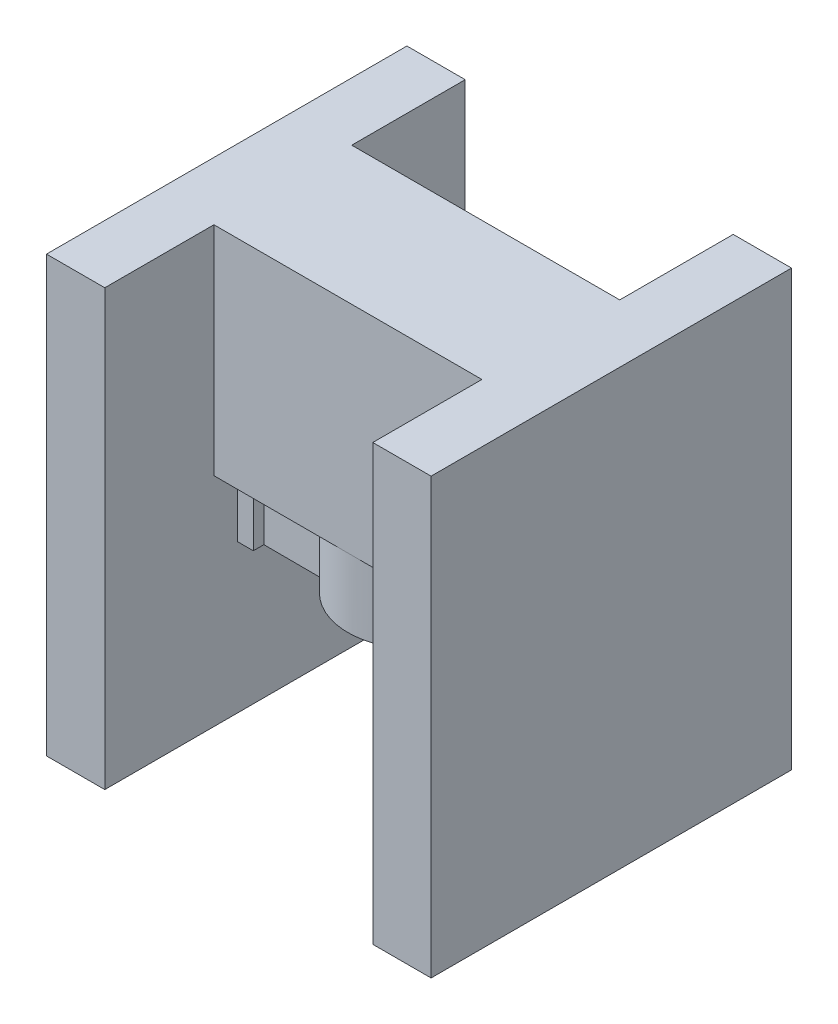
SolidWorks part; units mm, degrees
ref_plane "Front Plane" through (0, 0, 0) normal (0, 0, 1) x (1, 0, 0)
ref_plane "Top Plane" through (0, 0, 0) normal (0, 1, 0) x (1, 0, 0)
ref_plane "Right Plane" through (0, 0, 0) normal (1, 0, 0) x (0, 0, -1)
sketch "Sketch1" plane through (0, 0, 0) normal (0, 1, 0) x (1, 0, 0)
  line L0 (118.5, 375) -> (592.5, 375) construction
  line L1 (24.82, 34.4098) -> (19.2722, 34.4309)
  line L2 (19.2722, 34.4309) -> (19.2722, 33.4309)
  line L3 (17.7797, 42.2353) -> (19.2722, 42.2353)
  line L5 (17.7797, 33.4309) -> (19.2722, 33.4309)
  line L6 (19.2722, 42.2353) -> (19.2722, 40.86)
  line L7 (43.0607, 54.9144) -> (43.0607, 42.2353)
  line L8 (48.5607, 54.9144) -> (43.0607, 54.9144)
  line L9 (48.5607, 20.9144) -> (48.5607, 54.9144)
  line L10 (43.0607, 20.9144) -> (48.5607, 20.9144)
  line L11 (36.0204, 34.4098) -> (41.5682, 34.4309)
  line L13 (41.5682, 40.86) -> (36.1056, 40.86)
  line L14 (17.7797, 33.4309) -> (17.7797, 20.9144)
  line L15 (17.7797, 20.9144) -> (12.2797, 20.9144)
  line L16 (12.2797, 20.9144) -> (12.2797, 54.9144)
  line L17 (12.2797, 54.9144) -> (17.7797, 54.9144)
  line L18 (17.7797, 54.9144) -> (17.7797, 42.2353)
  line L20 (43.0607, 33.4309) -> (43.0607, 20.9144)
  line L24 (41.5682, 42.2353) -> (41.5682, 40.86)
  line L25 (43.0607, 33.4309) -> (41.5682, 33.4309)
  line L26 (43.0607, 42.2353) -> (41.5682, 42.2353)
  line L27 (41.5682, 34.4309) -> (41.5682, 33.4309)
  line L29 (19.2722, 40.86) -> (24.7348, 40.86)
  arc A2 (24.82, 34.4098) -> (36.0204, 34.4098) centre (30.4202, 37.7094) ccw
  arc A3 (36.1056, 40.86) -> (24.7348, 40.86) centre (30.4202, 37.7094) ccw
  dimension "D9" = 20.9144
  dimension "D2" = 6.5
  dimension "D5" = 12.2797
  dimension "D1" = 34
  dimension "D3" = 25.281
  dimension "D4" = 5.5
  dimension "D6" = 19.2722
  dimension "D7" = 24.7348
  dimension "D8" = 24.82
  dimension "D10" = 33.4309
  dimension "D11" = 34.4098
  dimension "D12" = 34.4309
  dimension "D15" = 42.2353
extrude "Boss-Extrude1" add sketch "Sketch1" along normal blind 13
sketch "Sketch2" plane through (0, 13, 0) normal (0, 1, 0) x (1, 0, 0)
  line L0 (12.2797, 54.9144) -> (12.2797, 20.9144)
  line L1 (12.2797, 20.9144) -> (17.7797, 20.9144)
  line L2 (17.7797, 20.9144) -> (17.7797, 33.4309)
  line L3 (17.7797, 42.2353) -> (19.2722, 42.2353)
  line L4 (19.2722, 42.2353) -> (19.2722, 40.86)
  line L5 (19.2722, 40.86) -> (24.7348, 40.86)
  line L6 (41.5607, 42.2353) -> (41.5682, 40.86)
  line L7 (43.0607, 54.9144) -> (48.5607, 54.9144)
  line L8 (24.82, 34.4098) -> (19.2722, 34.4309)
  line L9 (19.2722, 34.4309) -> (19.2722, 33.4309)
  line L10 (19.2722, 33.4309) -> (17.7797, 33.4309)
  line L11 (41.5682, 40.86) -> (36.1056, 40.86)
  line L12 (17.7797, 42.2353) -> (17.7797, 54.9144)
  line L13 (17.7797, 54.9144) -> (12.2797, 54.9144)
  line L14 (30.4202, 43.9341) -> (30.4202, 31.4846) construction
  line L15 (43.0607, 42.2353) -> (43.0607, 54.9144)
  line L16 (41.5607, 42.2353) -> (43.0607, 42.2353)
  line L18 (36.0204, 34.4098) -> (41.5682, 34.4309)
  line L19 (41.5682, 34.4309) -> (41.5607, 33.4309)
  line L23 (43.0607, 33.4309) -> (41.5607, 33.4309)
  line L24 (43.0607, 20.9144) -> (43.0607, 33.4309)
  line L25 (48.5607, 20.9144) -> (43.0607, 20.9144)
  line L26 (48.5607, 54.9144) -> (48.5607, 20.9144)
  arc A0 (24.82, 34.4098) -> (36.0204, 34.4098) centre (30.4202, 37.7094) ccw
  arc A2 (36.1056, 40.86) -> (24.7348, 40.86) centre (30.4202, 37.7094) ccw
extrude "Boss-Extrude3" add sketch "Sketch2" along normal blind 14
sketch "Sketch3" plane through (0, 0, 0) normal (0, -1, 0) x (-1, 0, 0)
  line L0 (-12.2797, 20.9144) -> (-12.2797, 54.9144)
  line L1 (-12.2797, 54.9144) -> (-17.7797, 54.9144)
  line L2 (-17.7797, 54.9144) -> (-17.7797, 20.9144)
  line L3 (-17.7797, 20.9144) -> (-12.2797, 20.9144)
  line L4 (-43.0607, 20.9144) -> (-43.0607, 54.9144)
  line L5 (-43.0607, 54.9144) -> (-48.5607, 54.9144)
  line L6 (-48.5607, 54.9144) -> (-48.5607, 20.9144)
  line L7 (-48.5607, 20.9144) -> (-43.0607, 20.9144)
extrude "Boss-Extrude4" add sketch "Sketch3" along normal blind 14
sketch "Sketch4" plane through (0, 0, 0) normal (0, -1, 0) x (1, 0, 0)
  circle A0 centre (30.4202, -37.7094) radius 2
extrude "Boss-Extrude5" add sketch "Sketch4" along normal blind 7
sketch "Sketch5" plane through (0, 27, 0) normal (0, 1, 0) x (1, 0, 0)
  line L1 (48.5607, 20.9144) -> (48.5607, 54.9144) construction
  line L2 (30.4202, 31.2094) -> (48.5607, 31.2094)
  line L5 (48.5607, 31.2094) -> (48.5607, 37.9144)
  line L6 (12.2797, 54.9144) -> (12.2797, 20.9144) construction
  line L8 (48.5607, 37.9144) -> (48.5607, 44.2094)
  line L9 (48.5607, 44.2094) -> (30.4202, 44.2094)
  line L11 (30.4202, 44.2094) -> (12.2797, 44.2094)
  line L14 (12.2797, 44.2094) -> (12.2797, 37.9144)
  line L17 (12.2797, 37.9144) -> (12.2797, 31.2094)
  line L18 (12.2797, 31.2094) -> (30.4202, 31.2094)
  arc A2 (24.82, 34.4098) -> (36.0204, 34.4098) centre (30.4202, 37.7094) ccw construction
  arc A3 (36.1056, 40.86) -> (24.7348, 40.86) centre (30.4202, 37.7094) ccw construction
extrude "Boss-Extrude6" add sketch "Sketch5" against normal blind 20.5
